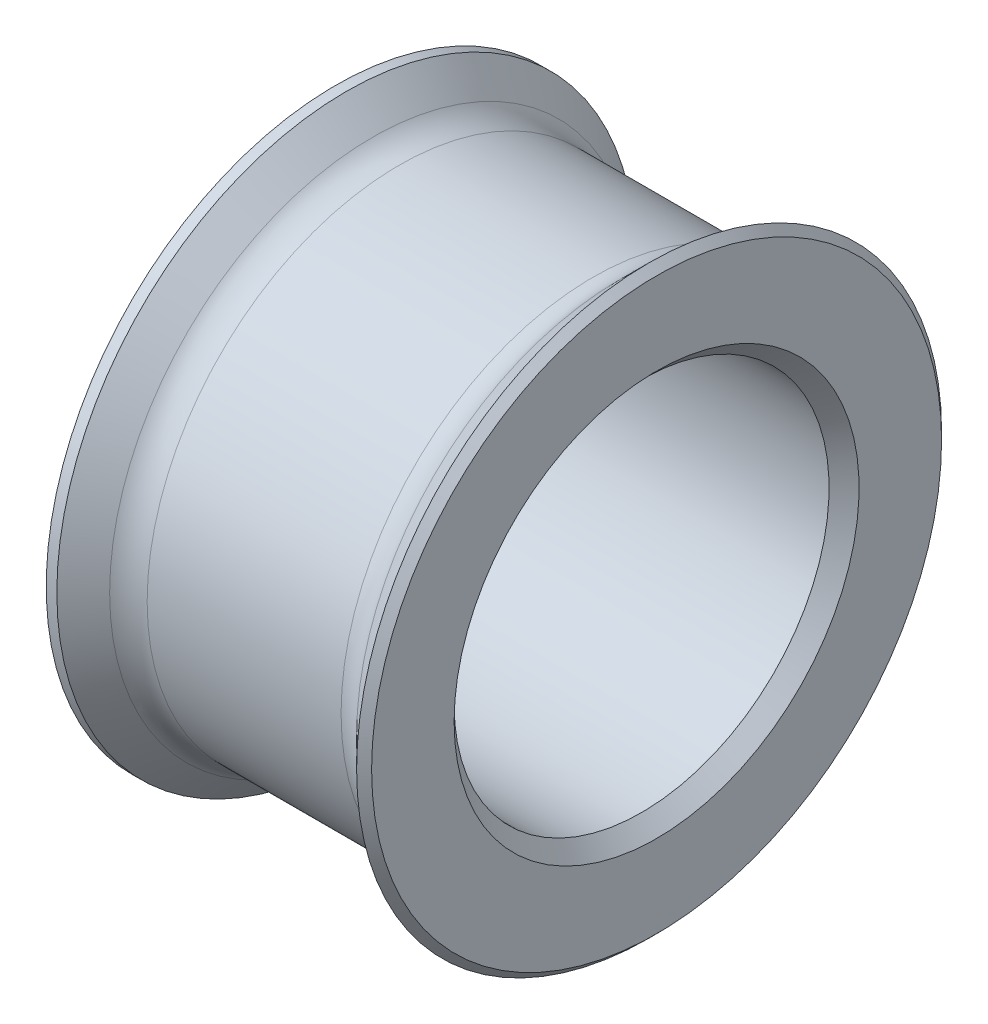
SolidWorks part; units mm, degrees
ref_plane "Front Plane" through (0, 0, 0) normal (0, 0, 1) x (1, 0, 0)
ref_plane "Top Plane" through (0, 0, 0) normal (0, 1, 0) x (1, 0, 0)
ref_plane "Right Plane" through (0, 0, 0) normal (1, 0, 0) x (0, 0, -1)
sketch "Sketch1" plane through (0, 0, 0) normal (0, 0, 1) x (1, 0, 0)
  line L0 (0, 3.36) -> (1.5, 3.36)
  line L1 (0, 3.36) -> (-1.5, 3.36)
  line L2 (-1.5, 3.36) -> (-2.14, 4)
  line L3 (1.5, 3.36) -> (2.14, 4)
  line L4 (2.14, 4) -> (2.14, 2.5)
  line L5 (2.14, 2.5) -> (-2.14, 2.5)
  line L6 (-2.14, 2.5) -> (-2.14, 4)
  line L7 (0, 0) -> (1.7715, 0) construction
  dimension "D1" = 1.5
  dimension "D2" = 2.5
  dimension "D3" = 135
  dimension "D4" = 135
  dimension "D5" = 0.86
  dimension "D6" = 1.5
revolve "Revolve1" add sketch "Sketch1" angle 360 about L7
chamfer "Chamfer1" distance 0.2 angle 45 4 edges at (-2.14, 0, 4) (-2.14, 0, 2.5) (2.14, 0, 2.5) (2.14, 0, 4)
fillet "Fillet1" radius 0.5 2 edges at (1.5, 0, 3.36) (-1.5, 0, 3.36)
